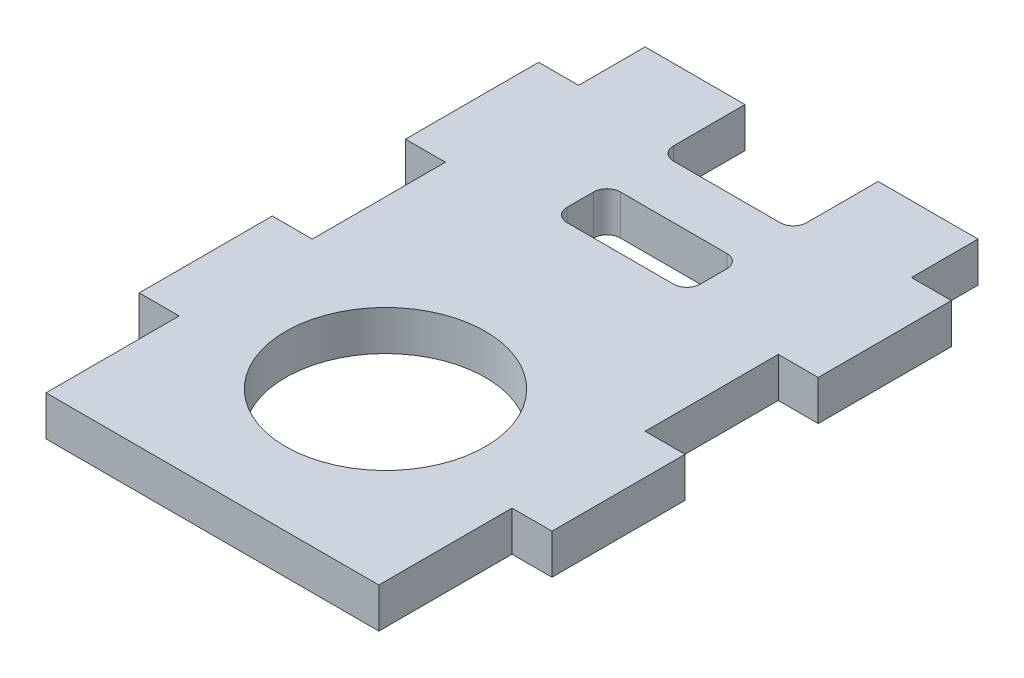
SolidWorks part; units mm, degrees
material "PC High Viscosity"
ref_plane "Front Plane" through (0, 0, 0) normal (0, 0, 1) x (1, 0, 0)
ref_plane "Top Plane" through (0, 0, 0) normal (0, 1, 0) x (1, 0, 0)
ref_plane "Right Plane" through (0, 0, 0) normal (1, 0, 0) x (0, 0, -1)
sketch "Sketch1" plane through (0, 0, 0) normal (0, 1, 0) x (1, 0, 0)
  line L1 (-12.5, -22.5) -> (12.5, -22.5)
  line L2 (-12.5, -22.5) -> (-12.5, 22.5)
  line L3 (-12.5, 22.5) -> (12.5, 22.5)
  line L4 (12.5, -22.5) -> (12.5, 22.5)
  line L5 (-12.5, -22.5) -> (12.5, 22.5) construction
  line L6 (-12.5, 22.5) -> (12.5, -22.5) construction
  line L9 (0, -22.5) -> (12.5, -22.5) construction
  line L10 (12.5, -10) -> (12.5, -22.5) construction
  point P0 (0, 0)
  dimension "D1" = 25
  dimension "D2" = 45
extrude "Boss-Extrude1" add sketch "Sketch1" along normal blind 3
sketch "Sketch2" plane through (0, 3, 0) normal (0, 1, 0) x (1, 0, 0)
  line L0 (12.5, 22.5) -> (-12.5, 22.5) construction
  line L1 (-5, 22.5) -> (5, 22.5)
  line L2 (-5, 22.5) -> (-5, 16.135)
  line L3 (-5, 16.135) -> (5, 16.135)
  line L4 (5, 22.5) -> (5, 16.135)
  line L5 (0, 16.135) -> (0, 22.5) construction
  line L7 (-5, 12.135) -> (5, 12.135)
  line L8 (-5, 12.135) -> (-5, 8.135)
  line L9 (-5, 8.135) -> (5, 8.135)
  line L10 (5, 12.135) -> (5, 8.135)
  circle A0 centre (0, -9.5) radius 7.5
  dimension "D1" = 15
  dimension "D2" = 10
  dimension "D3" = 6.365
  dimension "D4" = 32
  dimension "D5" = 4
  dimension "D6" = 4
extrude "Cut-Extrude1" cut sketch "Sketch2" against normal through all
fillet "Fillet1" radius 1 6 edges at (5, 1.5, -16.135) (-5, 1.5, -16.135) (5, 1.5, -8.135) (5, 1.5, -12.135) (-5, 1.5, -8.135) (-5, 1.5, -12.135)
sketch "Sketch3" plane through (0, 3, 0) normal (0, 1, 0) x (1, 0, 0)
  line L0 (12.5, -2.5) -> (15.5, -2.5)
  line L1 (12.5, 17.5) -> (15.5, 17.5)
  line L2 (12.5, 17.5) -> (12.5, 7.5)
  line L3 (12.5, 7.5) -> (15.5, 7.5)
  line L4 (15.5, 17.5) -> (15.5, 7.5)
  line L5 (15.5, -2.5) -> (15.5, -12.5)
  line L6 (12.5, -2.5) -> (12.5, -12.5)
  line L7 (12.5, -12.5) -> (15.5, -12.5)
  line L8 (12.5, -22.5) -> (12.5, -12.5) construction
  line L9 (12.5, -22.5) -> (12.5, 22.5) construction
  line L10 (0, -22.5) -> (0, 21.676) construction
  line L11 (-12.5, -22.5) -> (12.5, -22.5) construction
  line L12 (-12.5, -12.5) -> (-15.5, -12.5)
  line L13 (-12.5, -2.5) -> (-12.5, -12.5)
  line L14 (-15.5, -2.5) -> (-15.5, -12.5)
  line L15 (-12.5, -2.5) -> (-15.5, -2.5)
  line L16 (-15.5, 17.5) -> (-15.5, 7.5)
  line L17 (-12.5, 7.5) -> (-15.5, 7.5)
  line L18 (-12.5, 17.5) -> (-12.5, 7.5)
  line L19 (-12.5, 17.5) -> (-15.5, 17.5)
  point P30 (0, 0)
  dimension "D1" = 3
  dimension "D2" = 10
  dimension "D5" = 10
  dimension "D3" = 2
extrude "Boss-Extrude2" add sketch "Sketch3" against normal up to surface (3 mm away) up to face at (0, 0, -10.135)
equation "\"pulley_pitch_diam\"= 12.73mm"
equation "\"pulley_total_width\"= 16mm"
equation "\"pulley_total_diam\"= 16mm"
equation "\"belt_width\"= 6mm"
equation "\"material_thickness\"= 3mm"
equation "\"shaft_diam\"= 8mm"
equation "\"bearing_od\"= 22mm"
equation "\"bearing_thickness\"= 7mm"
equation "\"D1@Sketch3\"=\"material_thickness\""
